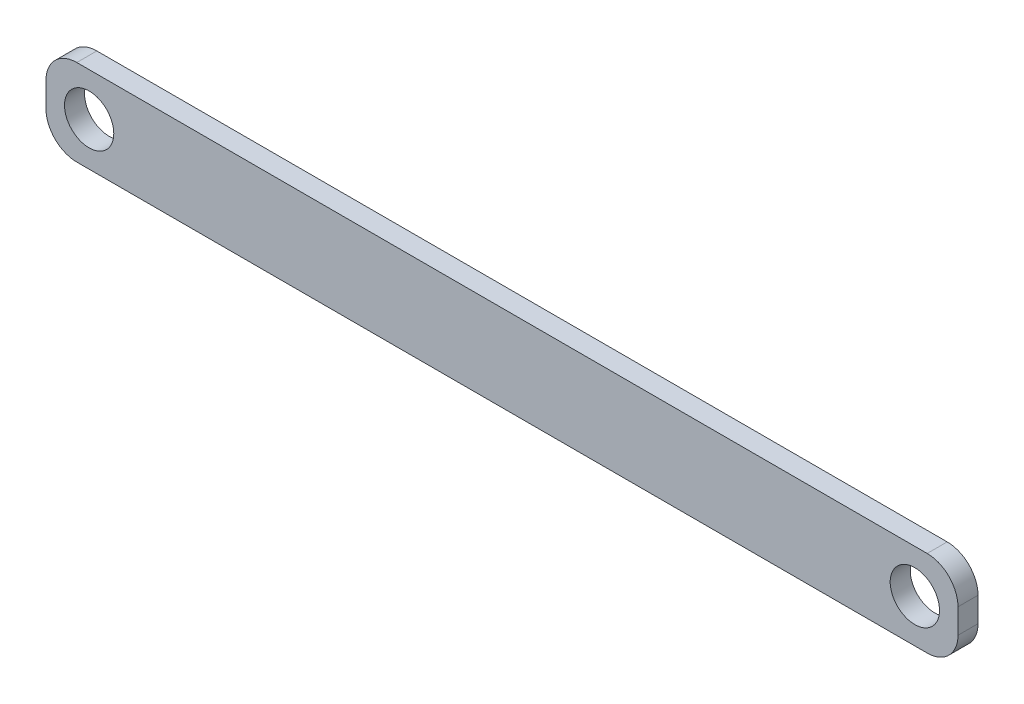
SolidWorks part; units mm, degrees
ref_plane "Front Plane" through (0, 0, 0) normal (0, 0, 1) x (1, 0, 0)
ref_plane "Top Plane" through (0, 0, 0) normal (0, 1, 0) x (1, 0, 0)
ref_plane "Right Plane" through (0, 0, 0) normal (1, 0, 0) x (0, 0, -1)
sketch "Sketch2" plane through (0, 0, 0) normal (0, 0, 1) x (1, 0, 0)
  line L1 (-148, -14) -> (148, -14)
  line L2 (-148, -14) -> (-148, 14)
  line L3 (-148, 14) -> (148, 14)
  line L4 (148, -14) -> (148, 14)
  line L5 (-148, -14) -> (148, 14) construction
  line L6 (-148, 14) -> (148, -14) construction
  circle A0 centre (-134, 0) radius 8
  circle A1 centre (134, 0) radius 8
  point P0 (0, 0)
  point P10 (0, 0)
  dimension "D3" = 16
  dimension "D1" = 28
  dimension "D2" = 296
  dimension "D4" = 268
  dimension "D5" = 134
extrude "Boss-Extrude1" add sketch "Sketch2" along normal blind 6.5
fillet "Fillet1" radius 10 4 edges at (-148, -14, 3.25) (-148, 14, 3.25) (148, -14, 3.25) (148, 14, 3.25)
